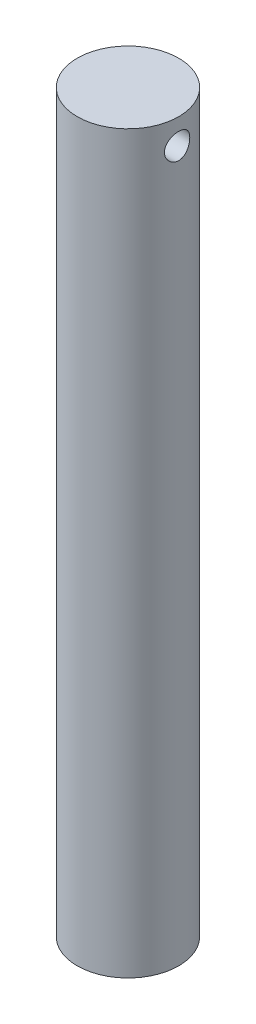
SolidWorks part; units mm, degrees
ref_plane "Front Plane" through (0, 0, 0) normal (0, 0, 1) x (1, 0, 0)
ref_plane "Top Plane" through (0, 0, 0) normal (0, 1, 0) x (1, 0, 0)
ref_plane "Right Plane" through (0, 0, 0) normal (1, 0, 0) x (0, 0, -1)
sketch "Sketch2" plane through (0, 0, 0) normal (0, 1, 0) x (1, 0, 0)
  circle A0 centre (0, 0) radius 12.7
  dimension "D1" = 25.4
extrude "Boss-Extrude3" add sketch "Sketch2" along normal blind 184.15
sketch "Sketch3" plane through (0, 0, 0) normal (1, 0, 0) x (0, 0, -1)
  line L1 (12.7, 184.15) -> (-12.7, 184.15) construction
  circle A0 centre (0, 177.8) radius 3.175
  dimension "D1" = 6.35
  dimension "D2" = 6.35
extrude "Cut-Extrude1" cut sketch "Sketch3" against normal through all and the other way through all
